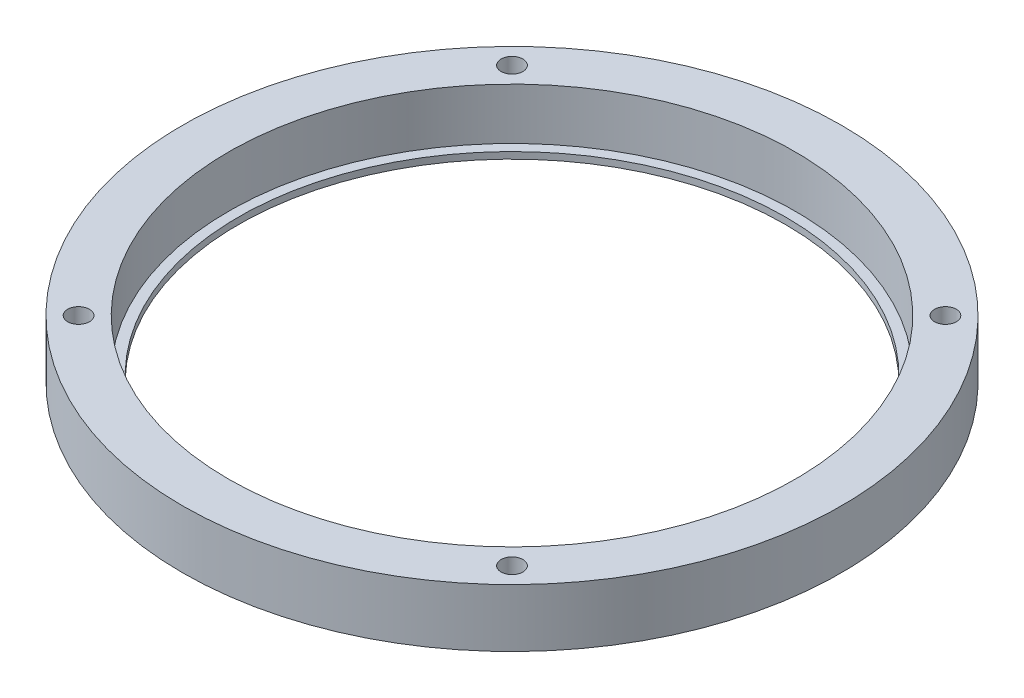
SolidWorks part; units mm, degrees
material "6061 合金"
ref_plane "前视基准面" through (0, 0, 0) normal (0, 0, 1) x (1, 0, 0)
ref_plane "上视基准面" through (0, 0, 0) normal (0, 1, 0) x (1, 0, 0)
ref_plane "右视基准面" through (0, 0, 0) normal (1, 0, 0) x (0, 0, -1)
sketch "草图2" plane through (0, 0, 0) normal (0, 1, 0) x (1, 0, 0)
  circle A0 centre (0, 0) radius 50
  circle A1 centre (0, 0) radius 43
  dimension "D1" = 100
  dimension "D2" = 86
extrude "凸台-拉伸1" add sketch "草图2" along normal blind 7.8
sketch "草图3" plane through (0, 0, 0) normal (0, -1, 0) x (1, 0, 0)
  circle A0 centre (0, 0) radius 41.5
  circle A1 centre (0, 0) radius 50
  circle A2 centre (0, 0) radius 50
  dimension "D2" = 83
  dimension "D1" = 0
extrude "凸台-拉伸2" add sketch "草图3" along normal blind 1
hole_wizard "M4 螺纹孔1" positions "草图4" profile "草图5" tap size "M4" standard "GB" end condition through all
sketch "草图4" plane through (0, 7.8, 0) normal (0, 1, 0) x (1, 0, 0)
  line L1 (-32.8805, 32.8805) -> (32.8805, 32.8805) construction
  line L2 (-32.8805, 32.8805) -> (-32.8805, -32.8805) construction
  line L3 (-32.8805, -32.8805) -> (32.8805, -32.8805) construction
  line L4 (32.8805, 32.8805) -> (32.8805, -32.8805) construction
  circle A0 centre (0, 0) radius 46.5 construction
  point P0 (-32.8805, 32.8805)
  point P2 (-32.8805, -32.8805)
  point P4 (32.8805, -32.8805)
  point P6 (32.8805, 32.8805)
  dimension "D1" = 93
cosmetic thread "孔螺蚊线1" parameters "D2"=4
cosmetic thread "孔螺蚊线2" parameters "D2"=4
cosmetic thread "孔螺蚊线3" parameters "D2"=4
cosmetic thread "孔螺蚊线4" parameters "D2"=4
sketch "草图5" plane through (-32.8805, 7.8, -32.8805) normal (1, 0, 0) x (0, 0, 1)
  line L0 (0, 0) -> (0, 8.8)
  line L1 (0, 8.8) -> (1.65, 8.8)
  line L2 (1.65, 8.8) -> (1.65, 0)
  line L5 (1.65, 0) -> (0, 0)
  line L11 (0, -6.35) -> (0, 107.95) construction
  dimension "通孔螺纹孔钻头直径" = 3.3
  dimension "通孔螺纹孔钻头深度" = 8.8
